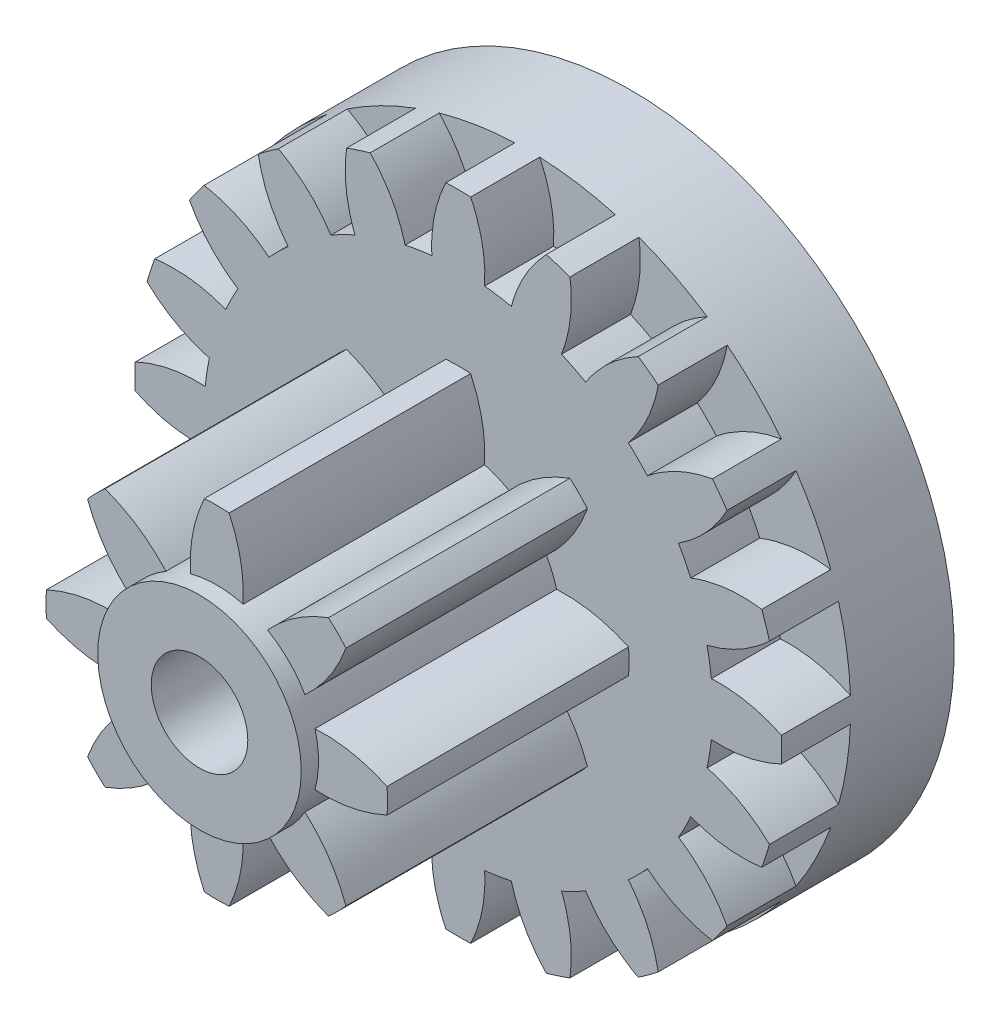
SolidWorks part; units mm, degrees
ref_plane "Front" through (0, 0, 0) normal (0, 0, 1) x (1, 0, 0)
ref_plane "Top" through (0, 0, 0) normal (0, 1, 0) x (1, 0, 0)
ref_plane "Right" through (0, 0, 0) normal (1, 0, 0) x (0, 0, -1)
sketch "草图1" plane through (0, 0, 0) normal (0, 0, 1) x (1, 0, 0)
  line L0 (0, 5.5081) -> (0, -0.6703) construction
  line L1 (0, 0) -> (-0.6106, 5.8096) construction
  line L2 (0, 0) -> (0.5998, 5.7068) construction
  arc A0 (-0.3826, 3.6676) -> (-0.7695, 3.6063) centre (0, 0) ccw
  arc A1 (0.18, 4.684) -> (-0.18, 4.684) centre (0, 0) ccw
  arc A3 (1.6186, 4.3992) -> (1.2763, 4.5104) centre (0, 0) ccw
  arc A4 (2.8988, 3.6837) -> (2.6076, 3.8953) centre (0, 0) ccw
  arc A5 (3.8953, 2.6076) -> (3.6837, 2.8988) centre (0, 0) ccw
  arc A6 (4.5104, 1.2763) -> (4.3992, 1.6186) centre (0, 0) ccw
  arc A7 (4.684, -0.18) -> (4.684, 0.18) centre (0, 0) ccw
  arc A8 (4.3992, -1.6186) -> (4.5104, -1.2763) centre (0, 0) ccw
  arc A9 (3.6837, -2.8988) -> (3.8953, -2.6076) centre (0, 0) ccw
  arc A10 (2.6076, -3.8953) -> (2.8988, -3.6837) centre (0, 0) ccw
  arc A11 (1.2763, -4.5104) -> (1.6186, -4.3992) centre (0, 0) ccw
  arc A12 (-0.18, -4.684) -> (0.18, -4.684) centre (0, 0) ccw
  arc A13 (-1.6186, -4.3992) -> (-1.2763, -4.5104) centre (0, 0) ccw
  arc A14 (-2.8988, -3.6837) -> (-2.6076, -3.8953) centre (0, 0) ccw
  arc A15 (-3.8953, -2.6076) -> (-3.6837, -2.8988) centre (0, 0) ccw
  arc A16 (-4.5104, -1.2763) -> (-4.3992, -1.6186) centre (0, 0) ccw
  arc A17 (-4.684, 0.18) -> (-4.684, -0.18) centre (0, 0) ccw
  arc A18 (-4.3992, 1.6186) -> (-4.5104, 1.2763) centre (0, 0) ccw
  arc A19 (-3.6837, 2.8988) -> (-3.8953, 2.6076) centre (0, 0) ccw
  arc A20 (-2.6076, 3.8953) -> (-2.8988, 3.6837) centre (0, 0) ccw
  arc A21 (-1.2763, 4.5104) -> (-1.6186, 4.3992) centre (0, 0) ccw
  arc A22 (0.7695, 3.6063) -> (0.3826, 3.6676) centre (0, 0) ccw
  arc A23 (1.8462, 3.192) -> (1.4972, 3.3699) centre (0, 0) ccw
  arc A24 (2.7422, 2.4653) -> (2.4653, 2.7422) centre (0, 0) ccw
  arc A25 (3.3699, 1.4972) -> (3.192, 1.8462) centre (0, 0) ccw
  arc A26 (3.6676, 0.3826) -> (3.6063, 0.7695) centre (0, 0) ccw
  arc A27 (3.6063, -0.7695) -> (3.6676, -0.3826) centre (0, 0) ccw
  arc A28 (3.192, -1.8462) -> (3.3699, -1.4972) centre (0, 0) ccw
  arc A29 (2.4653, -2.7422) -> (2.7422, -2.4653) centre (0, 0) ccw
  arc A30 (1.4972, -3.3699) -> (1.8462, -3.192) centre (0, 0) ccw
  arc A31 (-1.4972, 3.3699) -> (-1.8462, 3.192) centre (0, 0) ccw
  arc A32 (-2.4653, 2.7422) -> (-2.7422, 2.4653) centre (0, 0) ccw
  arc A33 (-3.192, 1.8462) -> (-3.3699, 1.4972) centre (0, 0) ccw
  arc A34 (-3.6063, 0.7695) -> (-3.6676, 0.3826) centre (0, 0) ccw
  arc A35 (-3.6676, -0.3826) -> (-3.6063, -0.7695) centre (0, 0) ccw
  arc A36 (-3.3699, -1.4972) -> (-3.192, -1.8462) centre (0, 0) ccw
  arc A37 (-2.7422, -2.4653) -> (-2.4653, -2.7422) centre (0, 0) ccw
  arc A38 (-1.8462, -3.192) -> (-1.4972, -3.3699) centre (0, 0) ccw
  arc A39 (-0.7695, -3.6063) -> (-0.3826, -3.6676) centre (0, 0) ccw
  arc A40 (0.3826, -3.6676) -> (0.7695, -3.6063) centre (0, 0) ccw
  spline S0 degree 2 poles (0.18, 4.684) (0.4125, 4.2014) (0.3826, 3.6676) knots 0 0 0 1 1 1
  spline S1 degree 2 poles (-0.18, 4.684) (-0.4125, 4.2014) (-0.3826, 3.6676) knots 0 0 0 1 1 1
  spline S2 degree 2 poles (1.2763, 4.5104) (0.906, 4.1233) (0.7695, 3.6063) knots 0 0 0 1 1 1
  spline S3 degree 2 poles (1.6186, 4.3992) (1.6907, 3.8683) (1.4972, 3.3699) knots 0 0 0 1 1 1
  spline S4 degree 2 poles (2.6076, 3.8953) (2.1358, 3.6415) (1.8462, 3.192) knots 0 0 0 1 1 1
  spline S5 degree 2 poles (2.8988, 3.6837) (2.8033, 3.1566) (2.4653, 2.7422) knots 0 0 0 1 1 1
  spline S6 degree 2 poles (3.6837, 2.8988) (3.1566, 2.8033) (2.7422, 2.4653) knots 0 0 0 1 1 1
  spline S7 degree 2 poles (3.8953, 2.6076) (3.6415, 2.1358) (3.192, 1.8462) knots 0 0 0 1 1 1
  spline S8 degree 2 poles (4.3992, 1.6186) (3.8683, 1.6907) (3.3699, 1.4972) knots 0 0 0 1 1 1
  spline S9 degree 2 poles (4.5104, 1.2763) (4.1233, 0.906) (3.6063, 0.7695) knots 0 0 0 1 1 1
  spline S10 degree 2 poles (4.684, 0.18) (4.2014, 0.4125) (3.6676, 0.3826) knots 0 0 0 1 1 1
  spline S11 degree 2 poles (4.684, -0.18) (4.2014, -0.4125) (3.6676, -0.3826) knots 0 0 0 1 1 1
  spline S12 degree 2 poles (4.5104, -1.2763) (4.1233, -0.906) (3.6063, -0.7695) knots 0 0 0 1 1 1
  spline S13 degree 2 poles (4.3992, -1.6186) (3.8683, -1.6907) (3.3699, -1.4972) knots 0 0 0 1 1 1
  spline S14 degree 2 poles (3.8953, -2.6076) (3.6415, -2.1358) (3.192, -1.8462) knots 0 0 0 1 1 1
  spline S15 degree 2 poles (3.6837, -2.8988) (3.1566, -2.8033) (2.7422, -2.4653) knots 0 0 0 1 1 1
  spline S16 degree 2 poles (2.8988, -3.6837) (2.8033, -3.1566) (2.4653, -2.7422) knots 0 0 0 1 1 1
  spline S17 degree 2 poles (2.6076, -3.8953) (2.1358, -3.6415) (1.8462, -3.192) knots 0 0 0 1 1 1
  spline S18 degree 2 poles (1.6186, -4.3992) (1.6907, -3.8683) (1.4972, -3.3699) knots 0 0 0 1 1 1
  spline S19 degree 2 poles (1.2763, -4.5104) (0.906, -4.1233) (0.7695, -3.6063) knots 0 0 0 1 1 1
  spline S20 degree 2 poles (0.18, -4.684) (0.4125, -4.2014) (0.3826, -3.6676) knots 0 0 0 1 1 1
  spline S21 degree 2 poles (-0.18, -4.684) (-0.4125, -4.2014) (-0.3826, -3.6676) knots 0 0 0 1 1 1
  spline S22 degree 2 poles (-1.2763, -4.5104) (-0.906, -4.1233) (-0.7695, -3.6063) knots 0 0 0 1 1 1
  spline S23 degree 2 poles (-1.6186, -4.3992) (-1.6907, -3.8683) (-1.4972, -3.3699) knots 0 0 0 1 1 1
  spline S24 degree 2 poles (-2.6076, -3.8953) (-2.1358, -3.6415) (-1.8462, -3.192) knots 0 0 0 1 1 1
  spline S25 degree 2 poles (-2.8988, -3.6837) (-2.8033, -3.1566) (-2.4653, -2.7422) knots 0 0 0 1 1 1
  spline S26 degree 2 poles (-3.6837, -2.8988) (-3.1566, -2.8033) (-2.7422, -2.4653) knots 0 0 0 1 1 1
  spline S27 degree 2 poles (-3.8953, -2.6076) (-3.6415, -2.1358) (-3.192, -1.8462) knots 0 0 0 1 1 1
  spline S28 degree 2 poles (-4.3992, -1.6186) (-3.8683, -1.6907) (-3.3699, -1.4972) knots 0 0 0 1 1 1
  spline S29 degree 2 poles (-4.5104, -1.2763) (-4.1233, -0.906) (-3.6063, -0.7695) knots 0 0 0 1 1 1
  spline S30 degree 2 poles (-4.684, -0.18) (-4.2014, -0.4125) (-3.6676, -0.3826) knots 0 0 0 1 1 1
  spline S31 degree 2 poles (-4.684, 0.18) (-4.2014, 0.4125) (-3.6676, 0.3826) knots 0 0 0 1 1 1
  spline S32 degree 2 poles (-4.5104, 1.2763) (-4.1233, 0.906) (-3.6063, 0.7695) knots 0 0 0 1 1 1
  spline S33 degree 2 poles (-4.3992, 1.6186) (-3.8683, 1.6907) (-3.3699, 1.4972) knots 0 0 0 1 1 1
  spline S34 degree 2 poles (-3.8953, 2.6076) (-3.6415, 2.1358) (-3.192, 1.8462) knots 0 0 0 1 1 1
  spline S35 degree 2 poles (-3.6837, 2.8988) (-3.1566, 2.8033) (-2.7422, 2.4653) knots 0 0 0 1 1 1
  spline S36 degree 2 poles (-2.8988, 3.6837) (-2.8033, 3.1566) (-2.4653, 2.7422) knots 0 0 0 1 1 1
  spline S37 degree 2 poles (-2.6076, 3.8953) (-2.1358, 3.6415) (-1.8462, 3.192) knots 0 0 0 1 1 1
  spline S38 degree 2 poles (-1.6186, 4.3992) (-1.6907, 3.8683) (-1.4972, 3.3699) knots 0 0 0 1 1 1
  spline S39 degree 2 poles (-1.2763, 4.5104) (-0.906, 4.1233) (-0.7695, 3.6063) knots 0 0 0 1 1 1
  point P7 (0, 4.6875)
  point P10 (0, 4.1875)
  point P11 (-0.18, 4.684)
  point P12 (0.18, 4.684)
  point P13 (-0.35, 4.1728)
  point P14 (0.35, 4.1728)
  point P15 (0, 3.6875)
  point P16 (-0.3826, 3.6676)
  point P17 (0.3826, 3.6676)
  point P137 (0, 0)
  dimension "D1" = 7.375
  dimension "D2" = 0.18
  dimension "D3" = 20
  dimension "D4" = 9.375
  dimension "D5" = 0.18
  dimension "D6" = 0.35
  dimension "D7" = 0.35
extrude "凸台-拉伸1" add sketch "草图1" along normal mid plane 1
sketch "草图2" plane through (0, 0, -0.5) normal (0, 0, -1) x (-1, 0, 0)
  circle A0 centre (0, 0) radius 1.25
  dimension "D1" = 2.5
extrude "凸台-拉伸2" add sketch "草图2" along normal blind 0.25
sketch "草图3" plane through (0, 0, 0.5) normal (0, 0, 1) x (1, 0, 0)
  line L0 (0, 0) -> (0, 2.741) construction
  line L1 (0, 0) -> (0.7513, 2.804) construction
  line L2 (0, 0) -> (-0.7709, 2.8771) construction
  arc A0 (-0.3832, 1.4243) -> (-0.7362, 1.2782) centre (0, 0) ccw
  arc A3 (0.1799, 2.4685) -> (-0.18, 2.4684) centre (0, 0) ccw
  arc A4 (1.8727, 1.6183) -> (1.6182, 1.8727) centre (0, 0) ccw
  arc A5 (2.4685, -0.1799) -> (2.4684, 0.18) centre (0, 0) ccw
  arc A6 (1.6183, -1.8727) -> (1.8727, -1.6182) centre (0, 0) ccw
  arc A7 (-0.1799, -2.4685) -> (0.18, -2.4684) centre (0, 0) ccw
  arc A8 (-1.8727, -1.6183) -> (-1.6182, -1.8727) centre (0, 0) ccw
  arc A9 (-2.4685, 0.1799) -> (-2.4684, -0.18) centre (0, 0) ccw
  arc A10 (-1.6183, 1.8727) -> (-1.8727, 1.6182) centre (0, 0) ccw
  arc A11 (0.7362, 1.2782) -> (0.3833, 1.4243) centre (0, 0) ccw
  arc A12 (-1.2782, 0.7362) -> (-1.4243, 0.3833) centre (0, 0) ccw
  arc A13 (-1.4243, -0.3832) -> (-1.2782, -0.7362) centre (0, 0) ccw
  arc A14 (-0.7362, -1.2782) -> (-0.3833, -1.4243) centre (0, 0) ccw
  arc A15 (0.3832, -1.4243) -> (0.7362, -1.2782) centre (0, 0) ccw
  arc A16 (1.2782, -0.7362) -> (1.4243, -0.3833) centre (0, 0) ccw
  arc A17 (1.4243, 0.3832) -> (1.2782, 0.7362) centre (0, 0) ccw
  spline S0 degree 2 poles (-0.18, 2.4684) (-0.41, 1.9709) (-0.3832, 1.4243) knots 0 0 0 1 1 1
  spline S1 degree 2 poles (0.1799, 2.4685) (0.4101, 1.971) (0.3833, 1.4243) knots 0 0 0 1 1 1
  spline S2 degree 2 poles (1.8727, 1.6183) (1.6836, 1.1037) (1.2782, 0.7362) knots 0 0 0 1 1 1
  spline S3 degree 2 poles (1.6182, 1.8727) (1.1037, 1.6836) (0.7362, 1.2782) knots 0 0 0 1 1 1
  spline S4 degree 2 poles (2.4685, -0.1799) (1.971, -0.4101) (1.4243, -0.3833) knots 0 0 0 1 1 1
  spline S5 degree 2 poles (2.4684, 0.18) (1.9709, 0.41) (1.4243, 0.3832) knots 0 0 0 1 1 1
  spline S6 degree 2 poles (1.6183, -1.8727) (1.1037, -1.6836) (0.7362, -1.2782) knots 0 0 0 1 1 1
  spline S7 degree 2 poles (1.8727, -1.6182) (1.6836, -1.1037) (1.2782, -0.7362) knots 0 0 0 1 1 1
  spline S8 degree 2 poles (-0.1799, -2.4685) (-0.4101, -1.971) (-0.3833, -1.4243) knots 0 0 0 1 1 1
  spline S9 degree 2 poles (0.18, -2.4684) (0.41, -1.9709) (0.3832, -1.4243) knots 0 0 0 1 1 1
  spline S10 degree 2 poles (-1.8727, -1.6183) (-1.6836, -1.1037) (-1.2782, -0.7362) knots 0 0 0 1 1 1
  spline S11 degree 2 poles (-1.6182, -1.8727) (-1.1037, -1.6836) (-0.7362, -1.2782) knots 0 0 0 1 1 1
  spline S12 degree 2 poles (-2.4685, 0.1799) (-1.971, 0.4101) (-1.4243, 0.3833) knots 0 0 0 1 1 1
  spline S13 degree 2 poles (-2.4684, -0.18) (-1.9709, -0.41) (-1.4243, -0.3832) knots 0 0 0 1 1 1
  spline S14 degree 2 poles (-1.6183, 1.8727) (-1.1037, 1.6836) (-0.7362, 1.2782) knots 0 0 0 1 1 1
  spline S15 degree 2 poles (-1.8727, 1.6182) (-1.6836, 1.1037) (-1.2782, 0.7362) knots 0 0 0 1 1 1
  point P5 (0, 1.475)
  point P9 (0.3833, 1.4243)
  point P10 (-0.3832, 1.4243)
  point P11 (0, 2.475)
  point P12 (-0.18, 2.4684)
  point P13 (0.1799, 2.4685)
  point P14 (0, 1.975)
  point P15 (-0.3486, 1.944)
  point P16 (0.3486, 1.944)
  point P64 (0, 0)
  dimension "D1" = 2.95
  dimension "D2" = 8
  dimension "D4" = 0.3832
  dimension "D5" = 0.3832
  dimension "D6" = 0.18
  dimension "D7" = 0.18
  dimension "D8" = 0.35
  dimension "D9" = 0.35
extrude "凸台-拉伸3" add sketch "草图3" along normal blind 3.5
sketch "草图4" plane through (0, 0, 0) normal (0, 0, 1) x (1, 0, 0)
  circle A0 centre (0, 0) radius 0.7
  dimension "D1" = 1.4
extrude "切除-拉伸1" cut sketch "草图4" against normal through all both and the other way through all
sketch "草图7" plane through (0, 0, 4) normal (0, 0, 1) x (1, 0, 0)
  circle A0 centre (0, 0) radius 1.475
  dimension "D1" = 2.95
extrude "凸台-拉伸5" add sketch "草图7" along normal blind 0.25
sketch "草图8" plane through (0, 0, 4.25) normal (0, 0, 1) x (1, 0, 0)
  circle A0 centre (0, 0) radius 0.7
  dimension "D1" = 1.4
extrude "切除-拉伸2" cut sketch "草图8" against normal through all
sketch "草图12" plane through (0, 0, -0.5) normal (0, 0, -1) x (-1, 0, 0)
  circle A0 centre (0, 0) radius 4.6875
  dimension "D1" = 9.375
extrude "凸台-拉伸6" add sketch "草图12" along normal blind 1.5
